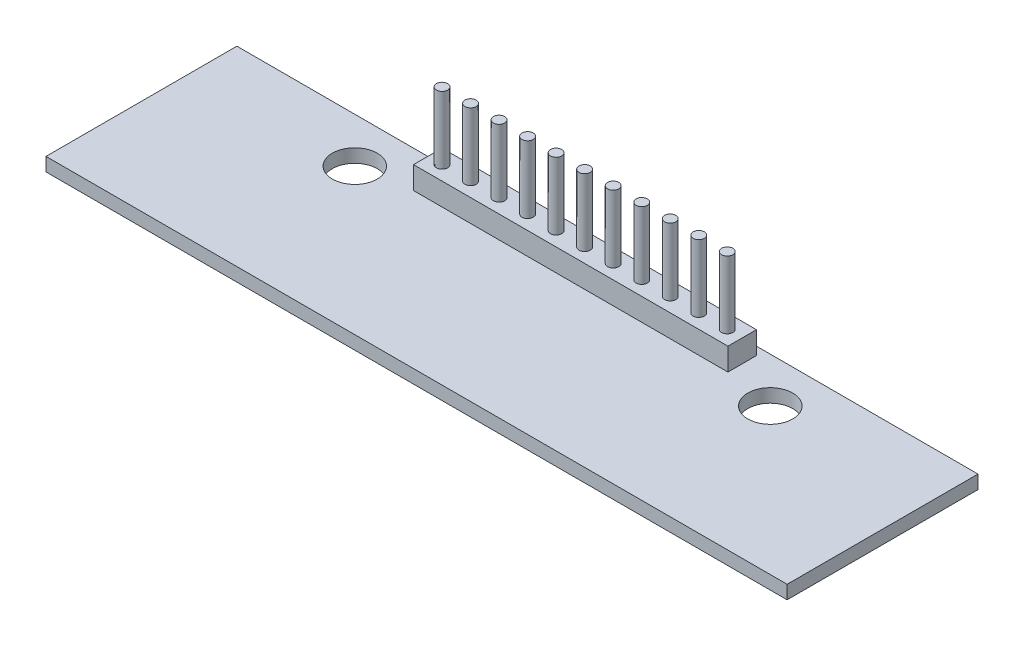
SolidWorks part; units mm, degrees
ref_plane "Front Plane" through (0, 0, 0) normal (0, 0, 1) x (1, 0, 0)
ref_plane "Top Plane" through (0, 0, 0) normal (0, 1, 0) x (1, 0, 0)
ref_plane "Right Plane" through (0, 0, 0) normal (1, 0, 0) x (0, 0, -1)
sketch "Sketch1" plane through (0, 0, 0) normal (0, 1, 0) x (1, 0, 0)
  line L0 (0, 8.5) -> (0, 4.5) construction
  line L1 (-33, 8.5) -> (33, 8.5)
  line L2 (-33, 8.5) -> (-33, -8.5)
  line L3 (-33, -8.5) -> (33, -8.5)
  line L4 (33, 8.5) -> (33, -8.5)
  line L5 (-33, 8.5) -> (33, -8.5) construction
  line L6 (-33, -8.5) -> (33, 8.5) construction
  line L7 (0, 4.5) -> (18.5, 4.5) construction
  circle A0 centre (18.5, 4.5) radius 2
  circle A1 centre (-18.5, 4.5) radius 2
  point P0 (0, 0)
  dimension "D5" = 4
  dimension "D1" = 17
  dimension "D2" = 66
  dimension "D3" = 4
  dimension "D4" = 18.5
extrude "Boss-Extrude1" add sketch "Sketch1" along normal blind 1.2
sketch "Sketch2" plane through (0, 1.2, 0) normal (0, 1, 0) x (1, 0, 0)
  line L0 (0, 8.5) -> (0, 6.5) construction
  line L1 (33, 8.5) -> (-33, 8.5) construction
  line L3 (-14, 7.77) -> (14, 7.77)
  line L4 (-14, 7.77) -> (-14, 5.23)
  line L5 (-14, 5.23) -> (14, 5.23)
  line L6 (14, 7.77) -> (14, 5.23)
  line L7 (-14, 7.77) -> (14, 5.23) construction
  line L8 (-14, 5.23) -> (14, 7.77) construction
  dimension "D1" = 2
  dimension "D2" = 2.54
  dimension "D3" = 28
extrude "Boss-Extrude2" add sketch "Sketch2" along normal blind 2
sketch "Sketch3" plane through (0, 3.2, 0) normal (0, 1, 0) x (1, 0, 0)
  line L0 (-14, 6.5) -> (-12.73, 6.5) construction
  line L1 (-14, 7.77) -> (-14, 5.23) construction
  circle A0 centre (-12.73, 6.5) radius 0.5
  circle A1 centre (-10.19, 6.5) radius 0.5
  circle A2 centre (-7.65, 6.5) radius 0.5
  circle A3 centre (-5.11, 6.5) radius 0.5
  circle A4 centre (-2.57, 6.5) radius 0.5
  circle A5 centre (-0.03, 6.5) radius 0.5
  circle A6 centre (2.51, 6.5) radius 0.5
  circle A7 centre (5.05, 6.5) radius 0.5
  circle A8 centre (7.59, 6.5) radius 0.5
  circle A9 centre (10.13, 6.5) radius 0.5
  circle A10 centre (12.67, 6.5) radius 0.5
  dimension "D2" = 1
  dimension "D1" = 1.27
  dimension "D3" = 11
extrude "Boss-Extrude3" add sketch "Sketch3" along normal blind 6
